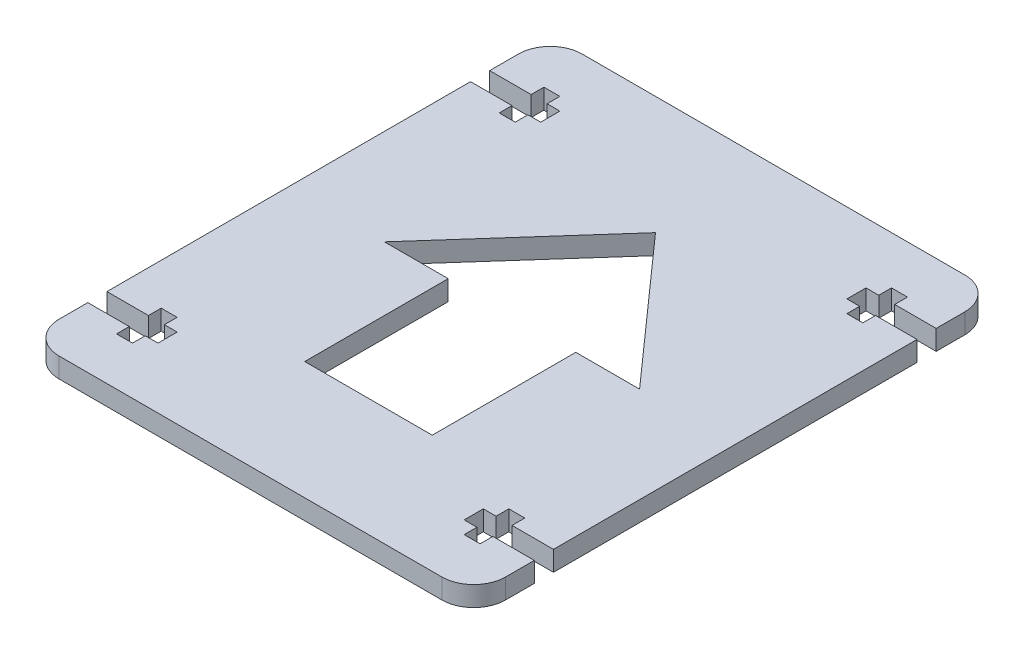
SolidWorks part; units mm, degrees
ref_plane "Front Plane" through (0, 0, 0) normal (0, 0, 1) x (1, 0, 0)
ref_plane "Top Plane" through (0, 0, 0) normal (0, 1, 0) x (1, 0, 0)
ref_plane "Right Plane" through (0, 0, 0) normal (1, 0, 0) x (0, 0, -1)
sketch "Sketch1" plane through (0, 0, 0) normal (0, 1, 0) x (1, 0, 0)
  line L0 (0, 30) -> (35, 30) construction
  line L1 (0, 41) -> (35, 41)
  line L2 (0, 41) -> (0, 0)
  line L3 (0, 0) -> (35, 0)
  line L4 (35, 41) -> (35, 31.5)
  line L5 (35, 31.5) -> (28.5, 31.5)
  line L6 (28.5, 31.5) -> (28.5, 33.5)
  line L7 (28.5, 33.5) -> (26, 33.5)
  line L8 (26, 33.5) -> (26, 31.5)
  line L9 (26, 31.5) -> (24, 31.5)
  line L10 (24, 31.5) -> (24, 28.5)
  line L11 (24, 28.5) -> (26, 28.5)
  line L12 (26, 28.5) -> (26, 26.5)
  line L13 (26, 26.5) -> (28.5, 26.5)
  line L14 (28.5, 26.5) -> (28.5, 28.5)
  line L15 (28.5, 28.5) -> (35, 28.5)
  line L16 (35, 28.5) -> (35, 0)
  point P17 (24, 30)
  dimension "D1" = 35
  dimension "D2" = 2.5
  dimension "D3" = 9
  dimension "D4" = 2
  dimension "D5" = 3
  dimension "D6" = 7.5
  dimension "D7" = 7
  dimension "D8" = 30
extrude "Boss-Extrude1" add sketch "Sketch1" along normal mid plane 3.125
mirror "Mirror1" about plane through (0, 0, 0) normal (1, 0, 0) of "Boss-Extrude1"
mirror "Mirror4" about plane through (0, 0, 0) normal (0, 0, 1) of "Mirror1", "Boss-Extrude1"
fillet "Fillet1" radius 5 4 edges at (-35, 0, -41) (35, 0, -41) (35, 0, 41) (-35, 0, 41)
sketch "Sketch2" plane through (0, 1.5625, 0) normal (0, 1, 0) x (1, 0, 0)
  line L0 (0, 22.5) -> (0, -22.5)
  line L1 (0, -22.5) -> (-10, -22.5)
  line L2 (-10, -22.5) -> (-10, 0)
  line L3 (-10, 0) -> (-20, 0)
  line L4 (-20, 0) -> (0, 22.5)
  dimension "D1" = 45
  dimension "D2" = 10
  dimension "D3" = 10
extrude "Cut-Extrude1" cut sketch "Sketch2" against normal through all both and the other way through all
mirror "Mirror5" about plane through (0, 0, 0) normal (1, 0, 0) of "Cut-Extrude1"
